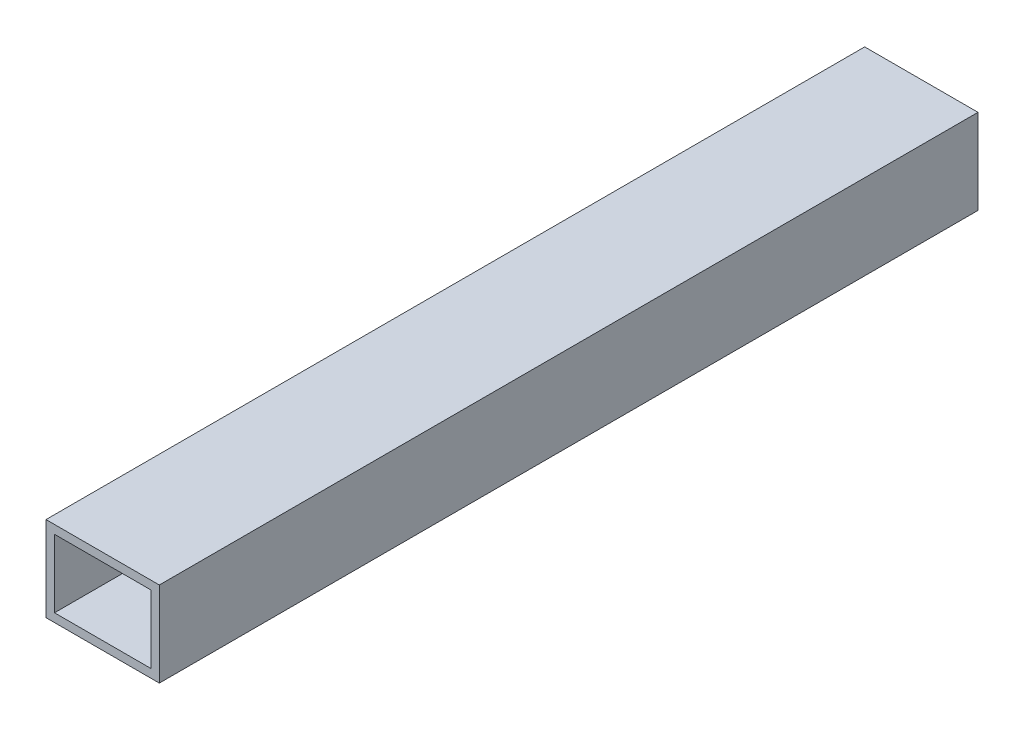
SolidWorks part; units mm, degrees
ref_plane "Front Plane" through (0, 0, 0) normal (0, 0, 1) x (1, 0, 0)
ref_plane "Top Plane" through (0, 0, 0) normal (0, 1, 0) x (1, 0, 0)
ref_plane "Right Plane" through (0, 0, 0) normal (1, 0, 0) x (0, 0, -1)
sketch "Croquis1" plane through (0, 0, 0) normal (1, 0, 0) x (0, 0, -1)
  line L0 (-144.5, -15) -> (-144.5, 15)
  line L1 (-144.5, -15) -> (144.5, -15)
  line L2 (-144.5, 15) -> (144.5, 15)
  line L3 (144.5, -15) -> (144.5, 15)
  line L4 (-144.5, -15) -> (144.5, 15) construction
  line L5 (-144.5, 15) -> (144.5, -15) construction
  point P1 (0, 0)
  dimension "D1" = 289
  dimension "D2" = 30
extrude "Saliente-Extruir1" add sketch "Croquis1" along normal blind 40
sketch "Croquis2" plane through (0, 0, 144.5) normal (0, 0, 1) x (1, 0, 0)
  line L0 (3, -12) -> (37, -12)
  line L1 (3, -12) -> (3, 12)
  line L2 (37, -12) -> (37, 12)
  line L3 (3, 12) -> (37, 12)
  line L4 (3, -12) -> (37, 12) construction
  line L5 (37, -12) -> (3, 12) construction
  line L6 (40, 15) -> (40, -15) construction
  line L7 (40, 15) -> (0, 15) construction
  line L8 (0, 15) -> (0, -15) construction
  line L9 (40, -15) -> (0, -15) construction
  point P1 (20, 0)
  dimension "D1" = 3
  dimension "D2" = 3
  dimension "D3" = 3
  dimension "D4" = 3
extrude "Cortar-Extruir1" cut sketch "Croquis2" against normal blind 890
